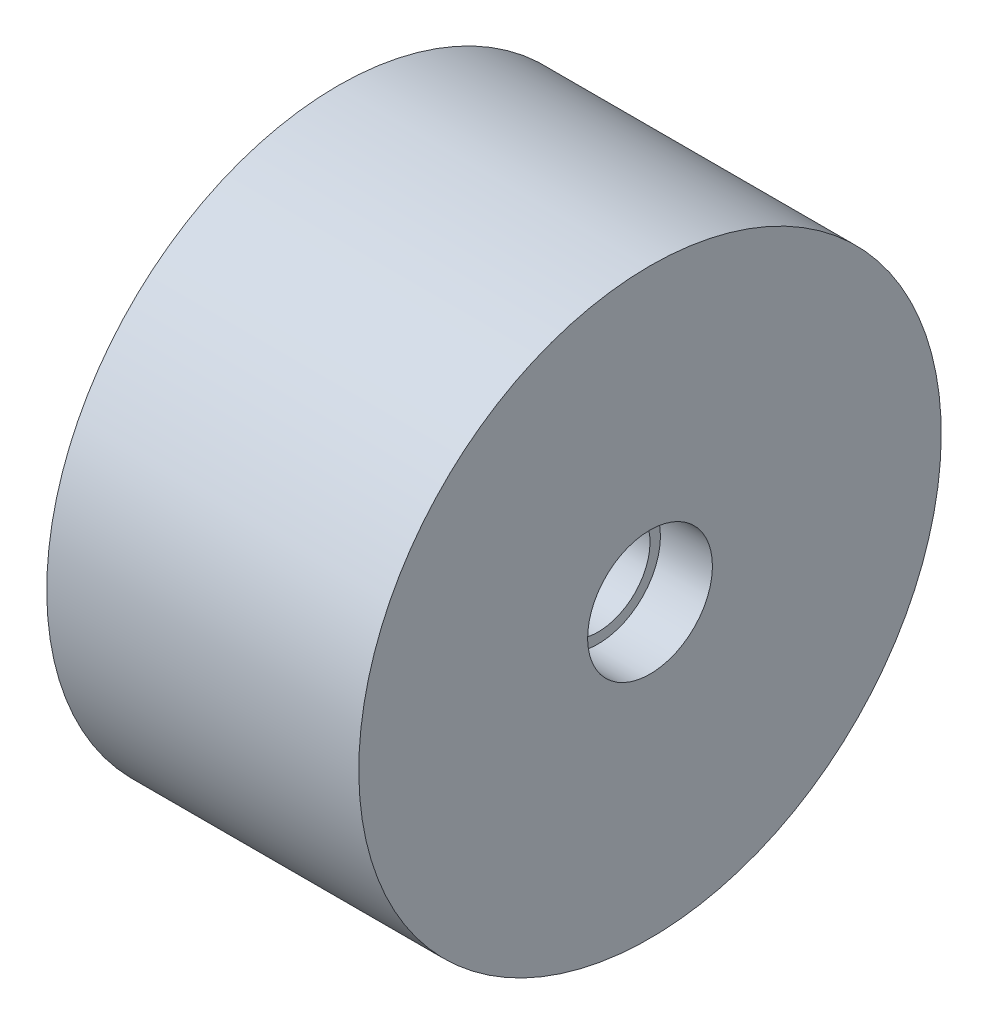
SolidWorks part; units mm, degrees
material "Polyetheretherketone (PEEK)"
ref_plane "Front Plane" through (0, 0, 0) normal (0, 0, 1) x (1, 0, 0)
ref_plane "Top Plane" through (0, 0, 0) normal (0, 1, 0) x (1, 0, 0)
ref_plane "Right Plane" through (0, 0, 0) normal (1, 0, 0) x (0, 0, -1)
sketch "Sketch1" plane through (0, 0, 0) normal (0, 0, 1) x (1, 0, 0)
  line L1 (0, 17) -> (0, 28)
  line L2 (0, 28) -> (-15, 28)
  line L3 (-15, 28) -> (-15, 27)
  line L4 (-15, 27) -> (-1, 27)
  line L5 (-1, 27) -> (-1, 18)
  line L11 (-14, 18) -> (-14, 17)
  line L12 (-1, 18) -> (-14, 18)
  line L13 (0, 17) -> (-2.5, 17)
  line L14 (-2.5, 17) -> (-2.5, 16.5)
  line L15 (-2.5, 16.5) -> (-12.45, 16.5)
  line L16 (-12.45, 16.5) -> (-12.45, 17)
  line L17 (-12.45, 17) -> (-14, 17)
  line L18 (0.9228, 14) -> (-15.5972, 14) construction
  dimension "D1" = 15
  dimension "D2" = 9.95
  dimension "D3" = 1
  dimension "D4" = 2.5
  dimension "D5" = 14
  dimension "D6" = 1
  dimension "D7" = 3
  dimension "D8" = 1.5
  dimension "D9" = 14
  dimension "D10" = 13
  dimension "D12" = 0
  dimension "D14" = 14
revolve "Revolve1" add sketch "Sketch1" angle 360 about L18
